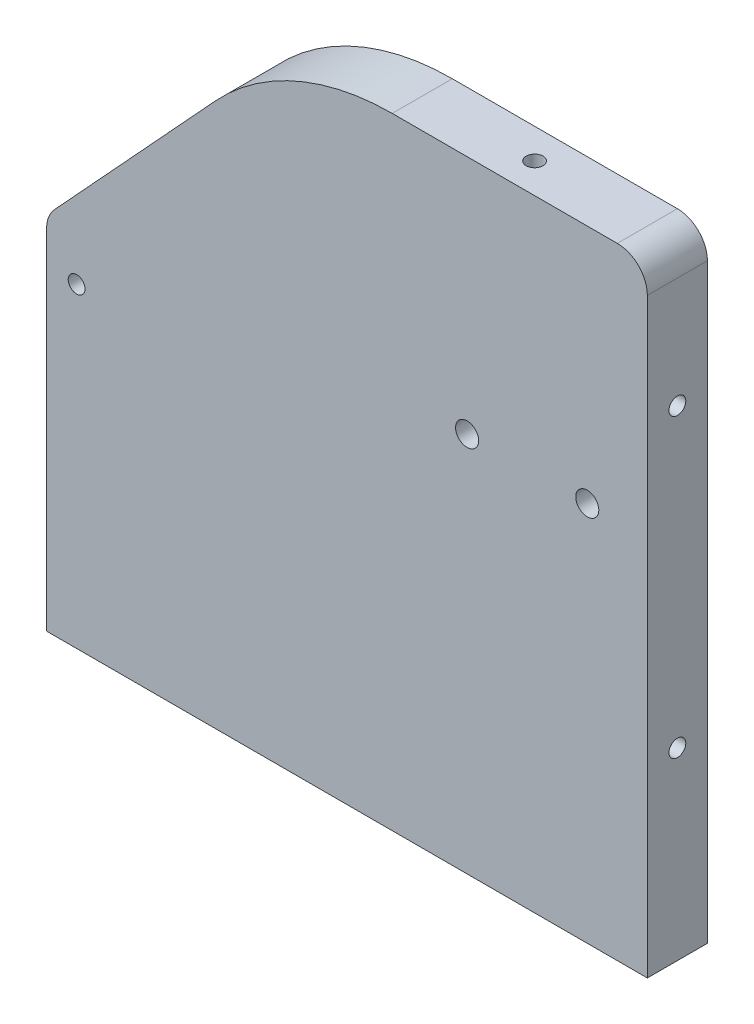
SolidWorks part; units mm, degrees
ref_plane "Front Plane" through (0, 0, 0) normal (0, 0, 1) x (1, 0, 0)
ref_plane "Top Plane" through (0, 0, 0) normal (0, 1, 0) x (1, 0, 0)
ref_plane "Right Plane" through (0, 0, 0) normal (1, 0, 0) x (0, 0, -1)
sketch "Sketch1" plane through (0, 0, 0) normal (0, 0, 1) x (1, 0, 0)
  line L0 (0, 38.1) -> (0, 0)
  line L1 (0, 0) -> (63.5, 0)
  line L2 (63.5, 0) -> (63.5, 65.659)
  line L3 (63.5, 65.659) -> (25.4, 65.659)
  line L4 (25.4, 65.659) -> (0, 38.1)
  dimension "D1" = 65.659
  dimension "D2" = 63.5
  dimension "D3" = 38.1
  dimension "D4" = 38.1
extrude "Boss-Extrude1" add sketch "Sketch1" along normal mid plane 6.35
fillet "Fillet1" radius 25.4 1 edges at (25.4, 65.659, 0)
fillet "Fillet2" radius 3.175 1 edges at (0, 38.1, 0)
fillet "Fillet3" radius 3.175 1 edges at (63.5, 65.659, 0)
hole_wizard "#2-56 Tapped Hole1" positions "Sketch3" profile "Sketch2" tap size "#2-56" standard "Ansi Inch"
sketch "Sketch3" plane through (63.5, 0, 0) normal (1, 0, 0) x (0, 0, -1)
  point P0 (0, 50.7961)
  point P4 (0, 19.477)
sketch "Sketch2" plane through (63.5, 50.7961, 0) normal (0, 1, 0) x (0, 0, -1)
  line L0 (0, 0) -> (0, 6.1222)
  line L1 (0, 6.1222) -> (0.889, 5.588)
  line L2 (0.889, 5.588) -> (0.889, 0)
  line L5 (0.889, 0) -> (0, 0)
  line L10 (0, 6.1222) -> (-0.889, 5.588) construction
  line L11 (0, -6.35) -> (0, 107.95) construction
  dimension "Tap Drill Dia." = 1.778
  dimension "Tap Drill Depth" = 5.588
  dimension "Drill Angle" = 118
cosmetic thread "Hole Thread1" parameters "D1"=4.318, "D2"=2.1844
cosmetic thread "Hole Thread2" parameters "D1"=4.318, "D2"=2.1844
hole_wizard "#2 Clearance Hole1" positions "Sketch11" profile "Sketch10" hole size "#2" standard "Ansi Inch"
sketch "Sketch11" plane through (0, 0, 3.175) normal (0, 0, 1) x (1, 0, 0)
  line L0 (0, 0) -> (63.5, 0) construction
  line L1 (63.5, 0) -> (63.5, 62.484) construction
  point P0 (57.15, 40.259)
  point P1 (44.45, 40.259)
  dimension "D1" = 12.7
  dimension "D2" = 40.259
  dimension "D3" = 6.35
sketch "Sketch10" plane through (57.15, 40.259, 3.175) normal (1, 0, 0) x (0, -1, 0)
  line L0 (0, 0) -> (0, 26.1326)
  line L1 (0, 26.1326) -> (1.2192, 25.4)
  line L2 (1.2192, 25.4) -> (1.2192, 0)
  line L5 (1.2192, 0) -> (0, 0)
  line L10 (0, 26.1326) -> (-1.2192, 25.4) construction
  line L11 (0, -6.35) -> (0, 107.95) construction
  dimension "Hole Dia." = 2.4384
  dimension "Hole Depth" = 25.4
  dimension "Drill Angle" = 118
sketch "Sketch12" plane through (0, 0, -3.175) normal (0, 0, -1) x (-1, 0, 0)
  line L0 (0, 36.86) -> (0, 0) construction
  line L1 (-1.5875, 25.4) -> (-3.175, 25.4)
  line L2 (-1.5875, 25.4) -> (-1.5875, 22.225)
  line L3 (-1.5875, 22.225) -> (-3.175, 22.225)
  line L4 (-3.175, 25.4) -> (-3.175, 22.225)
  line L5 (-1.5875, 25.4) -> (-3.175, 22.225) construction
  line L6 (-1.5875, 22.225) -> (-3.175, 25.4) construction
  line L7 (-1.5875, 12.7) -> (-3.175, 12.7)
  line L8 (-1.5875, 12.7) -> (-1.5875, 9.525)
  line L9 (-1.5875, 9.525) -> (-3.175, 9.525)
  line L10 (-3.175, 12.7) -> (-3.175, 9.525)
  line L11 (-1.5875, 12.7) -> (-3.175, 9.525) construction
  line L12 (-1.5875, 9.525) -> (-3.175, 12.7) construction
  line L13 (0, 0) -> (-63.5, 0) construction
  point P0 (-2.3813, 23.8125)
  point P5 (-2.3813, 11.1125)
  dimension "D1" = 3.175
  dimension "D2" = 1.5875
  dimension "D3" = 9.525
  dimension "D4" = 3.175
  dimension "D5" = 9.525
extrude "Cut-Extrude1" cut sketch "Sketch12" against normal blind 3.175
hole_wizard "#2-56 Tapped Hole2" positions "Sketch14" profile "Sketch13" tap size "#2-56" standard "Ansi Inch"
sketch "Sketch14" plane through (-18.9868, 17.4993, 0) normal (-0.7353, 0.6777, 0) x (0, 0, 1)
  point P0 (0, 41.8288)
sketch "Sketch13" plane through (9.3613, 48.257, 0) normal (0, 0, 1) x (-0.6777, -0.7353, 0)
  line L0 (0, 0) -> (0, 6.1222)
  line L1 (0, 6.1222) -> (0.889, 5.588)
  line L2 (0.889, 5.588) -> (0.889, 0)
  line L5 (0.889, 0) -> (0, 0)
  line L10 (0, 6.1222) -> (-0.889, 5.588) construction
  line L11 (0, -6.35) -> (0, 107.95) construction
  dimension "Tap Drill Dia." = 1.778
  dimension "Tap Drill Depth" = 5.588
  dimension "Drill Angle" = 118
cosmetic thread "Hole Thread3" parameters "D1"=4.318, "D2"=2.1844
hole_wizard "#2-56 Tapped Hole3" positions "Sketch16" profile "Sketch15" tap size "#2-56" standard "Ansi Inch"
sketch "Sketch16" plane through (0, 65.659, 0) normal (0, 1, 0) x (-1, 0, 0)
  point P0 (-48.407, 0)
sketch "Sketch15" plane through (48.407, 65.659, 0) normal (1, 0, 0) x (0, 0, 1)
  line L0 (0, 0) -> (0, 6.1222)
  line L1 (0, 6.1222) -> (0.889, 5.588)
  line L2 (0.889, 5.588) -> (0.889, 0)
  line L5 (0.889, 0) -> (0, 0)
  line L10 (0, 6.1222) -> (-0.889, 5.588) construction
  line L11 (0, -6.35) -> (0, 107.95) construction
  dimension "Tap Drill Dia." = 1.778
  dimension "Tap Drill Depth" = 5.588
  dimension "Drill Angle" = 118
cosmetic thread "Hole Thread4" parameters "D1"=4.318, "D2"=2.1844
hole_wizard "#2-56 Tapped Hole4" positions "Sketch18" profile "Sketch17" tap size "#2-56" standard "Ansi Inch"
sketch "Sketch18" plane through (0, 0, 3.175) normal (0, 0, 1) x (1, 0, 0)
  line L0 (0, 36.86) -> (0, 0) construction
  line L1 (0, 0) -> (63.5, 0) construction
  point P0 (3.175, 33.3375)
  point P8 (-37.3543, 32.1766)
  dimension "D1" = 3.175
  dimension "D2" = 33.3375
sketch "Sketch17" plane through (3.175, 33.3375, 3.175) normal (1, 0, 0) x (0, -1, 0)
  line L0 (0, 0) -> (0, 11.2022)
  line L1 (0, 11.2022) -> (0.889, 10.668)
  line L2 (0.889, 10.668) -> (0.889, 0)
  line L5 (0.889, 0) -> (0, 0)
  line L10 (0, 11.2022) -> (-0.889, 10.668) construction
  line L11 (0, -6.35) -> (0, 107.95) construction
  dimension "Tap Drill Dia." = 1.778
  dimension "Tap Drill Depth" = 10.668
  dimension "Drill Angle" = 118
cosmetic thread "Hole Thread5" parameters "D1"=4.318, "D2"=2.1844
